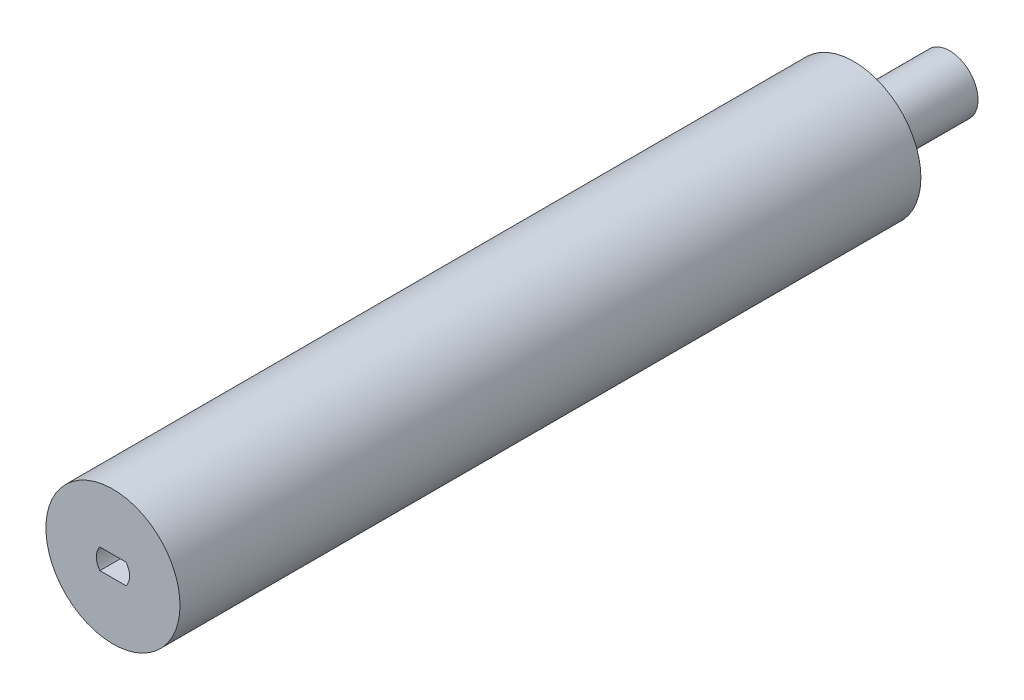
SolidWorks part; units mm, degrees
ref_plane "Front Plane" through (0, 0, 0) normal (0, 0, 1) x (1, 0, 0)
ref_plane "Top Plane" through (0, 0, 0) normal (0, 1, 0) x (1, 0, 0)
ref_plane "Right Plane" through (0, 0, 0) normal (1, 0, 0) x (0, 0, -1)
sketch "Sketch1" plane through (0, 0, 0) normal (0, 0, 1) x (1, 0, 0)
  line L10 (2.0511, -1.5674) -> (-2.0477, -1.5674)
  line L11 (2.0511, 1.6326) -> (-2.0477, 1.6326)
  arc A12 (-2.0477, 1.6326) -> (-2.0477, -1.5674) centre (0.0017, 0.0326) ccw
  arc A13 (2.0511, -1.5674) -> (2.0511, 1.6326) centre (0.0017, 0.0326) ccw
  point P8 (0, 1.5)
  point P11 (0, -1.5)
sketch "Sketch2" plane through (0, 0, 0) normal (0, 0, 1) x (1, 0, 0)
  circle A0 centre (0, 0) radius 10.5
  dimension "D1" = 21
extrude "Boss-Extrude1" add sketch "Sketch2" against normal blind 116
sketch "Sketch3" plane through (0, 0, -116) normal (0, 0, -1) x (-1, 0, 0)
  circle A0 centre (0, 0) radius 4.45
  dimension "D1" = 8.9
extrude "Boss-Extrude2" add sketch "Sketch3" along normal blind 15
extrude "Cut-Extrude1" cut sketch "Sketch1" against normal blind 10
